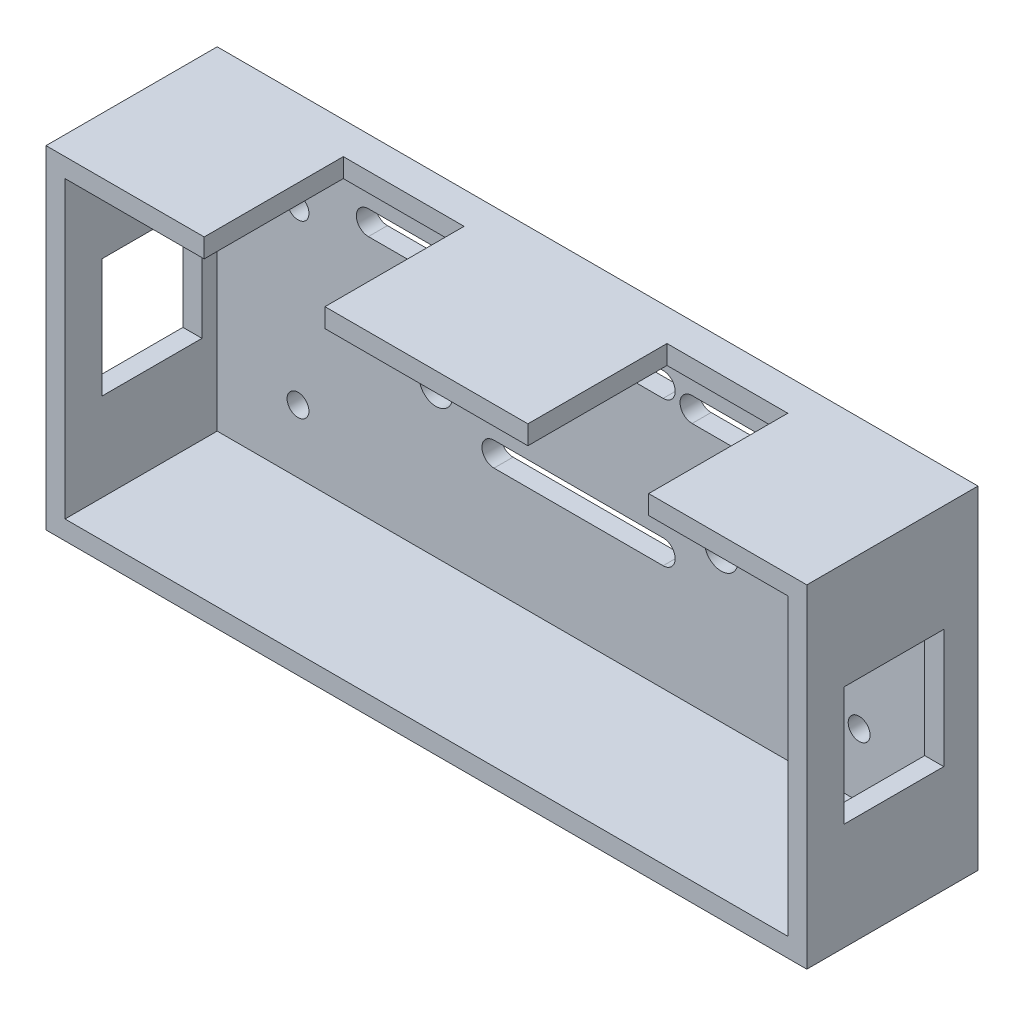
SolidWorks part; units mm, degrees
ref_plane "前视基准面" through (0, 0, 0) normal (0, 0, 1) x (1, 0, 0)
ref_plane "上视基准面" through (0, 0, 0) normal (0, 1, 0) x (1, 0, 0)
ref_plane "右视基准面" through (0, 0, 0) normal (1, 0, 0) x (0, 0, -1)
sketch "草图1" plane through (0, 0, 0) normal (0, 0, 1) x (1, 0, 0)
  line L1 (-40, 17.5) -> (40, 17.5)
  line L2 (-40, 17.5) -> (-40, -17.5)
  line L3 (-40, -17.5) -> (40, -17.5)
  line L4 (40, 17.5) -> (40, -17.5)
  line L5 (-40, 17.5) -> (40, -17.5) construction
  line L6 (-40, -17.5) -> (40, 17.5) construction
  point P0 (0, 0)
  dimension "D1" = 80
  dimension "D2" = 35
extrude "凸台-拉伸1" add sketch "草图1" along normal blind 2
sketch "草图2" plane through (0, 0, 2) normal (0, 0, 1) x (1, 0, 0)
  line L0 (-40, 17.5) -> (-40, -17.5) construction
  line L1 (-38, 15.5) -> (38, 15.5)
  line L2 (-38, 15.5) -> (-38, -15.5)
  line L3 (-38, -15.5) -> (38, -15.5)
  line L4 (38, 15.5) -> (38, -15.5)
  line L5 (-38, 15.5) -> (38, -15.5) construction
  line L6 (-38, -15.5) -> (38, 15.5) construction
  line L7 (40, 17.5) -> (-40, 17.5) construction
  line L12 (40, -17.5) -> (40, 17.5)
  line L13 (40, 17.5) -> (-40, 17.5)
  line L14 (-40, 17.5) -> (-40, -17.5)
  line L15 (-40, -17.5) -> (40, -17.5)
  line L16 (40, -17.5) -> (40, 17.5)
  line L17 (40, 17.5) -> (-40, 17.5)
  line L18 (-40, 17.5) -> (-40, -17.5)
  line L19 (-40, -17.5) -> (40, -17.5)
  point P0 (0, 0)
  dimension "D1" = 2
  dimension "D2" = 2
  dimension "D3" = 0
extrude "凸台-拉伸2" add sketch "草图2" along normal blind 16
sketch "草图3" plane through (-40, 0, 0) normal (-1, 0, 0) x (0, 0, 1)
  line L0 (0, 17.5) -> (0, -17.5) construction
  line L1 (3.6, 6.25) -> (14.1, 6.25)
  line L2 (3.6, 6.25) -> (3.6, -6.25)
  line L3 (3.6, -6.25) -> (14.1, -6.25)
  line L4 (14.1, 6.25) -> (14.1, -6.25)
  line L6 (18, 17.5) -> (0, 17.5) construction
  dimension "D1" = 3.6
  dimension "D2" = 10.5
  dimension "D3" = 12.5
  dimension "D4" = 11.25
extrude "切除-拉伸1" cut sketch "草图3" against normal through all
sketch "草图4" plane through (0, 0, 2) normal (0, 0, 1) x (1, 0, 0)
  line L0 (-40, 17.5) -> (-40, -17.5) construction
  line L1 (40, -17.5) -> (40, 17.5) construction
  circle A0 centre (-29.5, 9.1403) radius 1.15
  circle A1 centre (-29.5, -8.8597) radius 1.15
  circle A2 centre (29.5, 9.1403) radius 1.15
  circle A3 centre (29.5, -8.8597) radius 1.15
  circle A4 centre (-15, 0) radius 1.75
  circle A5 centre (15, 0) radius 1.75
  dimension "D3" = 2.3
  dimension "D4" = 2.3
  dimension "D5" = 2.3
  dimension "D6" = 2.3
  dimension "D9" = 3.5
  dimension "D10" = 3.5
  dimension "D1" = 18
  dimension "D2" = 18
  dimension "D7" = 10.5
  dimension "D8" = 10.5
  dimension "D11" = 15
  dimension "D12" = 15
extrude "切除-拉伸2" cut sketch "草图4" against normal through all
sketch "草图5" plane through (0, 0, 0) normal (0, 0, -1) x (-1, 0, 0)
  line L0 (-8.89, 12.198) -> (8.89, 12.198) construction
  line L1 (-8.89, 13.468) -> (8.89, 13.468)
  line L2 (-8.89, 10.928) -> (8.89, 10.928)
  line L3 (-40, 17.5) -> (40, 17.5) construction
  line L4 (-8.89, -3.042) -> (8.89, -3.042) construction
  line L5 (-8.89, -1.772) -> (8.89, -1.772)
  line L6 (-8.89, -4.312) -> (8.89, -4.312)
  line L7 (-22.098, 11.436) -> (-11.938, 11.436) construction
  line L8 (-22.098, 12.706) -> (-11.938, 12.706)
  line L9 (-22.098, 10.166) -> (-11.938, 10.166)
  line L10 (11.94, 11.436) -> (22.1, 11.436) construction
  line L11 (11.94, 12.706) -> (22.1, 12.706)
  line L12 (11.94, 10.166) -> (22.1, 10.166)
  arc A0 (-8.89, 13.468) -> (-8.89, 10.928) centre (-8.89, 12.198) ccw
  arc A1 (8.89, 10.928) -> (8.89, 13.468) centre (8.89, 12.198) ccw
  arc A2 (-8.89, -1.772) -> (-8.89, -4.312) centre (-8.89, -3.042) ccw
  arc A3 (8.89, -4.312) -> (8.89, -1.772) centre (8.89, -3.042) ccw
  arc A4 (-22.098, 12.706) -> (-22.098, 10.166) centre (-22.098, 11.436) ccw
  arc A5 (-11.938, 10.166) -> (-11.938, 12.706) centre (-11.938, 11.436) ccw
  arc A6 (11.94, 12.706) -> (11.94, 10.166) centre (11.94, 11.436) ccw
  arc A7 (22.1, 10.166) -> (22.1, 12.706) centre (22.1, 11.436) ccw
  point P2 (0, 12.198)
  point P9 (0, -3.042)
  point P17 (-17.018, 11.436)
  point P26 (17.02, 11.436)
  dimension "D2" = 1.27
  dimension "D4" = 1.27
  dimension "D8" = 1.27
  dimension "D1" = 5.302
  dimension "D3" = 17.78
  dimension "D5" = 20.542
  dimension "D6" = 17.78
  dimension "D7" = 17.018
  dimension "D9" = 10.16
  dimension "D10" = 6.064
  dimension "D11" = 1.27
  dimension "D12" = 10.16
  dimension "D13" = 17.02
extrude "切除-拉伸3" cut sketch "草图5" against normal through all
sketch "草图6" plane through (0, 17.5, 0) normal (0, 1, 0) x (1, 0, 0)
  line L0 (40, 0) -> (-40, 0) construction
  line L1 (-23.368, -3.37) -> (-10.668, -3.37)
  line L2 (-23.368, -3.37) -> (-23.368, -6.37)
  line L3 (-23.368, -6.37) -> (-10.668, -6.37)
  line L4 (-10.668, -3.37) -> (-10.668, -6.37)
  line L5 (10.67, -3.37) -> (23.37, -3.37)
  line L6 (10.67, -3.37) -> (10.67, -6.37)
  line L7 (10.67, -6.37) -> (23.37, -6.37)
  line L8 (23.37, -3.37) -> (23.37, -6.37)
  dimension "D1" = 10.668
  dimension "D2" = 10.67
  dimension "D3" = 12.7
  dimension "D4" = 12.7
  dimension "D5" = 3
  dimension "D6" = 3
  dimension "D7" = 3.37
  dimension "D8" = 3.37
extrude "切除-拉伸4" cut sketch "草图6" against normal up to next
sketch "草图7" plane through (0, 17.5, 0) normal (0, 1, 0) x (1, 0, 0)
  line L0 (40, -18) -> (-40, -18) construction
  line L1 (-23.368, -6.37) -> (-10.668, -6.37)
  line L2 (-23.368, -6.37) -> (-23.368, -18)
  line L3 (-23.368, -18) -> (-10.668, -18)
  line L4 (-10.668, -6.37) -> (-10.668, -18)
  line L5 (-10.668, -6.37) -> (-10.668, -3.37) construction
  line L6 (10.67, -6.37) -> (23.37, -6.37)
  line L7 (10.67, -6.37) -> (10.67, -18)
  line L8 (10.67, -18) -> (23.37, -18)
  line L9 (23.37, -6.37) -> (23.37, -18)
  line L10 (23.37, -6.37) -> (23.37, -3.37) construction
extrude "切除-拉伸5" cut sketch "草图7" against normal up to next
